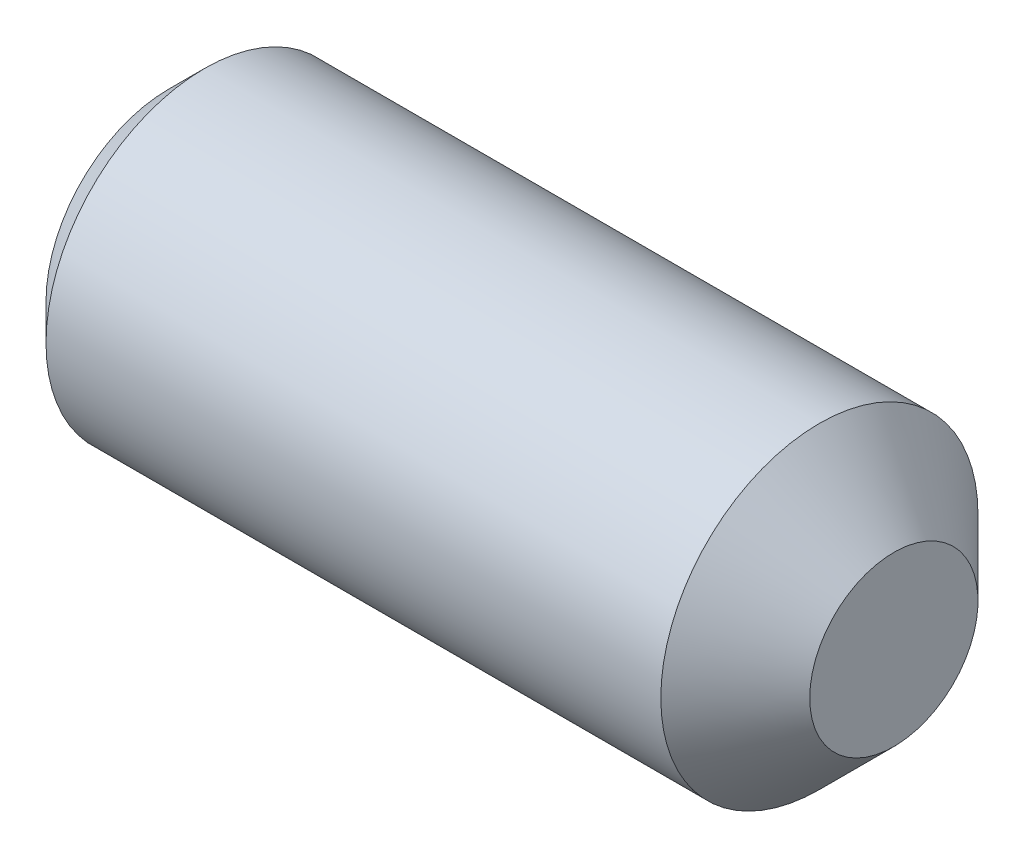
SolidWorks part; units mm, degrees
ref_plane "Plane1" through (0, 0, 0) normal (0, 0, 1) x (1, 0, 0)
ref_plane "Plane2" through (0, 0, 0) normal (0, 1, 0) x (1, 0, 0)
ref_plane "Plane3" through (0, 0, 0) normal (1, 0, 0) x (0, 0, -1)
sketch "BodySke" plane through (0, 0, 0) normal (0, 0, 1) x (1, 0, 0)
  line L0 (0, 0) -> (0, 1.6104)
  line L1 (0, 1.6104) -> (0.4724, 2.0828)
  line L2 (0.4724, 2.0828) -> (8.5471, 2.0828)
  line L3 (8.5471, 2.0828) -> (9.525, 1.1049)
  line L4 (9.525, 0) -> (0, 0)
  line L5 (-12.7, 0) -> (88.9, 0) construction
  line L6 (9.525, 1.1049) -> (9.525, 0)
  line L7 (9.525, 1.1049) -> (9.525, 10.6299) construction
  line L8 (0, -1.6104) -> (0.4724, -2.0828) construction
  line L9 (0.7925, 15.875) -> (0.7925, -3.175) construction
  line L10 (8.5471, -2.0828) -> (9.525, -1.1049) construction
  dimension "Length" = 9.525
  dimension "Diameter" = 4.1656
  dimension "Drive_ch_ang" = 45
  dimension "Minor_dia" = 3.2207
  dimension "Cup_nose_ang" = 45
  dimension "Cup_dia" = 2.2098
  dimension "Advance" = 0.7925
revolve "BaseBody" add sketch "BodySke" angle 360 about L5
cosmetic thread "ThreadCosmetic" [suppressed] parameters "Thread_minor"=3.2207
sketch "Sketch2" plane through (0, 0, 0) normal (-1, 0, 0) x (0, 0, 1)
  line L0 (0.5719, 0.9906) -> (-0.5719, 0.9906)
  line L1 (-0.5719, 0.9906) -> (-1.1438, 0)
  line L2 (0.5719, 0.9906) -> (1.1438, 0)
  line L3 (0.5719, -0.9906) -> (1.1438, 0)
  line L4 (0.5719, -0.9906) -> (-0.5719, -0.9906)
  line L5 (-0.5719, -0.9906) -> (-1.1438, 0)
  dimension "Hex_size" = 1.9812
  dimension "D2" = 0.9906
  dimension "D3" = 0.9906
extrude "Hex" cut sketch "Sketch2" against normal blind 2.286
sketch "Sketch4" plane through (0, 4.7709, -0.5249) normal (-1, 0, 0) x (0, 0, 1)
  line L0 (0.5249, -4.7709) -> (1.7695, -4.7709)
  line L1 (0.5249, -4.7709) -> (6.6732, -1.2211) construction
  line L2 (0.5249, -4.7709) -> (1.1472, -3.693)
  line L3 (1.5334, -4.5112) -> (1.7149, -4.4064)
  line L4 (1.254, -4.0273) -> (1.4355, -3.9225)
  arc A0 (1.5334, -4.5112) -> (1.254, -4.0273) centre (0.5249, -4.7709) ccw
  arc A1 (1.7695, -4.7709) -> (1.7149, -4.4064) centre (0.5249, -4.7709) ccw
  arc A2 (1.1472, -3.693) -> (1.4355, -3.9225) centre (0.5249, -4.7709) cw
  circle A3 centre (0.5249, -4.7709) radius 1.0414 construction
  circle A4 centre (0.5249, -4.7709) radius 1.2446 construction
  dimension "D1" = 30
  dimension "Spline_n_dim" = 2.0828
  dimension "Spline_m_dim" = 2.4892
  dimension "Spline_a_dim" = 60
  dimension "D3" = 0.2794
  dimension "Spline_p_dim" = 0.5588
extrude "Spline" [suppressed] cut sketch "Sketch4" against normal blind 2.032
pattern_circular "CirPattern1" [suppressed] count 6 every 60 about axis through (-12.7, 0, 0) along (1, 0, 0)
sketch "ThdSchSke" plane through (0, 0, 0) normal (0, 0, 1) x (1, 0, 0)
  line L0 (0.4724, -1.6104) -> (0.1416, -2.0828)
  line L1 (0.4724, -1.6104) -> (0.8032, -2.0828)
  line L2 (0.8032, -2.0828) -> (0.8032, -2.6035)
  line L3 (-3.175, 0) -> (5.1513, 0) construction
  line L4 (0.4724, 2.0828) -> (0.4724, -2.0828) construction
  line L5 (0.8032, -2.6035) -> (0.1416, -2.6035)
  line L6 (0.1416, -2.6035) -> (0.1416, -2.0828)
  dimension "Thread_minor" = 3.2207
  dimension "Diameter" = 4.1656
  dimension "SideAngle" = 55
  dimension "VeeAngle" = 70
  dimension "Overcut" = 5.207
revolve "ThreadSchematic" [suppressed] cut sketch "ThdSchSke" angle 360 about L3
pattern_linear "ThdSchPat" [suppressed]
equation "\"D2@Sketch2\" = \"Hex_size@Sketch2\" / 2"
equation "\"D3@Sketch2\" = \"Hex_size@Sketch2\" / 2"
equation "\"Thread_minor@ThreadCosmetic\" = \"Minor_dia@BodySke\""
equation "\"D1@Sketch4\" = \"Spline_a_dim@Sketch4\" / 2"
equation "\"D3@Sketch4\" = \"Spline_p_dim@Sketch4\" / 2"
equation "\"D2@CirPattern1\" = \"Spline_a_dim@Sketch4\""
equation "\"Num_teeth@CirPattern1\" = 360 / \"D2@CirPattern1\""
equation "\"Thread_minor@ThdSchSke\" = \"Thread_minor@ThreadCosmetic\""
equation "\"Diameter@ThdSchSke\" = \"Diameter@BodySke\""
equation "\"Overcut@ThdSchSke\" = \"Diameter@BodySke\" * 1.25"
equation "\"Num_threads@ThdSchPat\" = int( (\"Length@BodySke\" - ( ( ( \"Diameter@BodySke\" - \"Minor_dia@BodySke\" ) * 0.5 ) / tan( \"Drive_ch_ang@BodySke\" * 0.017453292 ) ) - ( ( ( \"Diameter@BodySke\" - \"Cup_dia@BodySke\" ) * 0.5 ) * tan( \"Cup_nose_ang@BodySke\" * 0.017453292 ) ) ) / \"Advance@BodySke\" + 0.999 )  + 1"
equation "\"Advance@ThdSchPat\" = (\"Length@BodySke\" - ( ( ( \"Diameter@BodySke\" - \"Minor_dia@BodySke\" ) * 0.5 ) / tan( \"Drive_ch_ang@BodySke\" * 0.017453292 ) ) - ( ( ( \"Diameter@BodySke\" - \"Cup_dia@BodySke\" ) * 0.5 ) * tan( \"Cup_nose_ang@BodySke\" * 0.017453292 ) ) ) /  (\"Num_threads@ThdSchPat\" - 1) 'relax it"
equation "' \"Num_threads@ThdSchPat\" = \"Num_threads@ThdSchPat\" - sgn( \"Num_threads@ThdSchPat\" - 1) '---chamfered tips only---"
